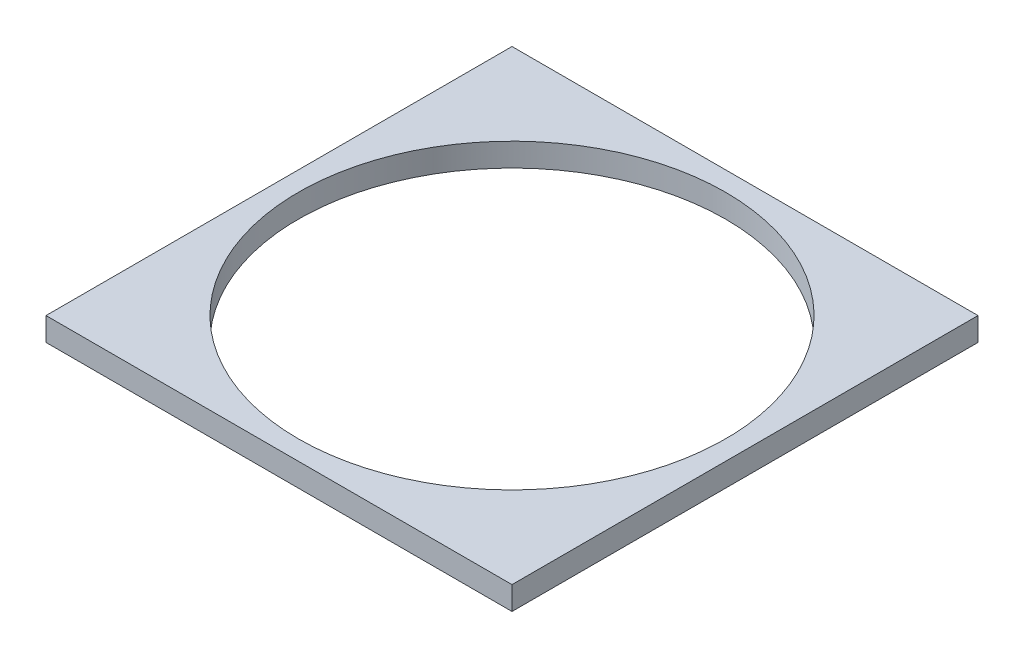
SolidWorks part; units mm, degrees
material "6061-T6 (SS)"
ref_plane "Front Plane" through (0, 0, 0) normal (0, 0, 1) x (1, 0, 0)
ref_plane "Top Plane" through (0, 0, 0) normal (0, 1, 0) x (1, 0, 0)
ref_plane "Right Plane" through (0, 0, 0) normal (1, 0, 0) x (0, 0, -1)
sketch "Sketch2" plane through (0, 0, 0) normal (0, 1, 0) x (1, 0, 0)
  line L1 (-76.2, 76.2) -> (76.2, 76.2)
  line L2 (-76.2, 76.2) -> (-76.2, -76.2)
  line L3 (-76.2, -76.2) -> (76.2, -76.2)
  line L4 (76.2, 76.2) -> (76.2, -76.2)
  line L5 (-76.2, 76.2) -> (76.2, -76.2) construction
  line L6 (-76.2, -76.2) -> (76.2, 76.2) construction
  circle A0 centre (0, 0) radius 69.85
  point P0 (0, 0)
  dimension "D3" = 139.7
  dimension "D1" = 152.4
  dimension "D2" = 152.4
extrude "Boss-Extrude1" add sketch "Sketch2" along normal blind 7.62
